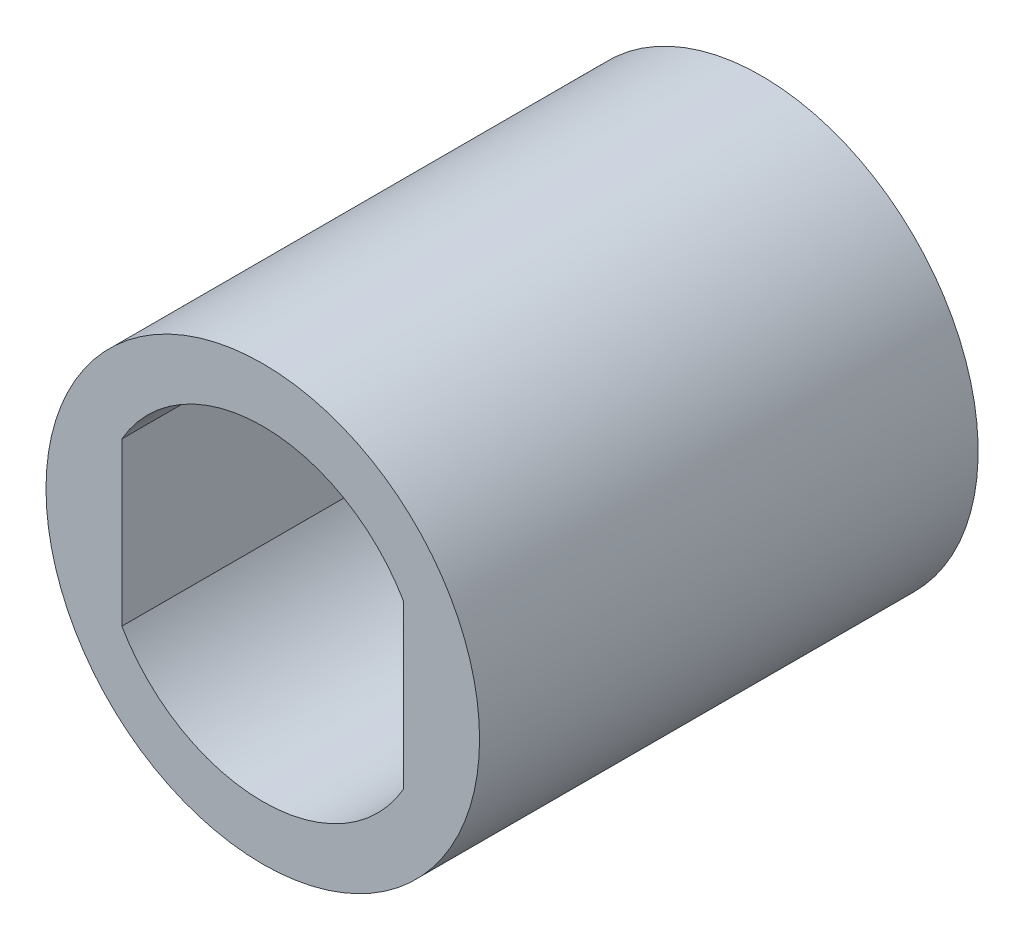
SolidWorks part; units mm, degrees
ref_plane "Front" through (0, 0, 0) normal (0, 0, 1) x (1, 0, 0)
ref_plane "Top" through (0, 0, 0) normal (0, 1, 0) x (1, 0, 0)
ref_plane "Right" through (0, 0, 0) normal (1, 0, 0) x (0, 0, -1)
sketch "Sketch1" plane through (0, 0, 0) normal (0, 0, 1) x (1, 0, 0)
  line L0 (-6.5, 3.7417) -> (-6.5, -3.7417)
  line L1 (0, 12.551) -> (0, -11.7205) construction
  line L2 (6.5, 3.7417) -> (6.5, -3.7417)
  circle A0 centre (0, 0) radius 10
  arc A1 (-6.5, -3.7417) -> (6.5, -3.7417) centre (0, 0) ccw
  arc A2 (6.5, 3.7417) -> (-6.5, 3.7417) centre (0, 0) ccw
  dimension "D1" = 20
  dimension "D2" = 15
  dimension "D3" = 13
extrude "Boss-Extrude1" add sketch "Sketch1" along normal blind 18
sketch "Sketch2" plane through (0, 0, 0) normal (0, 0, -1) x (-1, 0, 0)
  line L1 (0, 13.5081) -> (0, -12.7869) construction
  circle A0 centre (0, 0) radius 10
  circle A1 centre (0, 0) radius 4
  dimension "D1" = 20
  dimension "D2" = 8
extrude "Boss-Extrude2" add sketch "Sketch2" along normal blind 5
